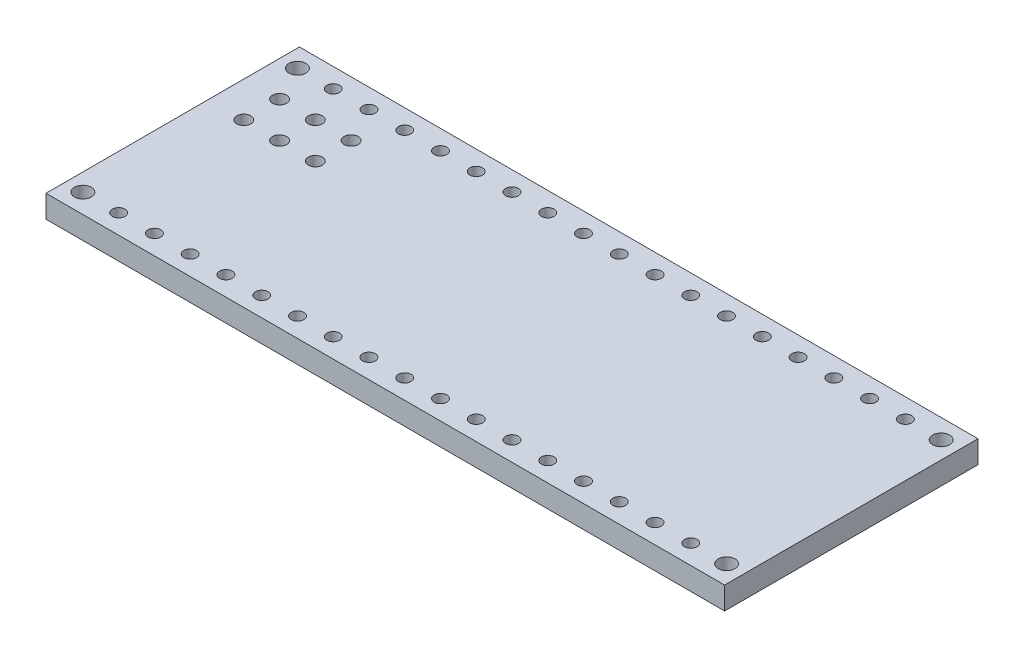
SolidWorks part; units mm, degrees
material "E-Glass Fiber"
ref_plane "Front Plane" through (0, 0, 0) normal (0, 0, 1) x (1, 0, 0)
ref_plane "Top Plane" through (0, 0, 0) normal (0, 1, 0) x (1, 0, 0)
ref_plane "Right Plane" through (0, 0, 0) normal (1, 0, 0) x (0, 0, -1)
sketch "Sketch1" plane through (0, 0, 0) normal (0, 1, 0) x (1, 0, 0)
  line L0 (0, 7.62) -> (-3.78, 7.62) construction
  line L1 (-3.78, 16.62) -> (44.42, 16.62)
  line L2 (-3.78, 16.62) -> (-3.78, -1.38)
  line L3 (-3.78, -1.38) -> (44.42, -1.38)
  line L4 (44.42, 16.62) -> (44.42, -1.38)
  line L5 (0, 0) -> (40.64, 0) construction
  line L6 (0, 0) -> (0, 15.24) construction
  line L7 (0, 15.24) -> (40.64, 15.24) construction
  line L8 (40.64, 0) -> (40.64, 15.24) construction
  line L10 (40.64, 7.62) -> (44.42, 7.62) construction
  circle A0 centre (-2.54, 0) radius 0.6
  circle A1 centre (-2.54, 15.24) radius 0.6
  circle A2 centre (43.18, 15.24) radius 0.6
  circle A3 centre (43.18, 0) radius 0.6
  dimension "D5" = 1.2
  dimension "D1" = 48.2
  dimension "D2" = 18
  dimension "D3" = 15.24
  dimension "D4" = 40.64
  dimension "D6" = 2.54
  dimension "D7" = 2.54
  dimension "D8" = 3.78
  dimension "D9" = 3.78
extrude "Boss-Extrude2" add sketch "Sketch1" along normal blind 1.6
sketch "Sketch2" plane through (0, 0, 0) normal (0, 1, 0) x (1, 0, 0)
  line L0 (0, -0.88) -> (0, 0.88) construction
  line L2 (-0.88, 0) -> (0.88, 0) construction
  circle A0 centre (0, 0) radius 0.45
  circle A1 centre (0, 15.24) radius 0.45
  dimension "D1" = 0.9
  dimension "D2" = 15.24
extrude "Cut-Extrude2" cut sketch "Sketch2" along normal blind 1.6
pattern_linear "LPattern1" count 17 spacing 2.54 along (1, 0, 0) of "Cut-Extrude2"
sketch "Sketch3" plane through (0, 0, 0) normal (0, 1, 0) x (1, 0, 0)
  line L1 (-0.88, 0) -> (0.88, 0) construction
  circle A0 centre (1.27, 12.7) radius 0.5
  circle A1 centre (-1.27, 12.7) radius 0.5
  circle A2 centre (-1.27, 10.16) radius 0.5
  circle A3 centre (3.81, 12.7) radius 0.5
  circle A4 centre (3.81, 10.16) radius 0.5
  circle A5 centre (1.27, 10.16) radius 0.5
  circle A6 centre (0, 15.24) radius 0.45 construction
  dimension "D1" = 1
  dimension "D5" = 10.16
  dimension "D7" = 2.54
  dimension "D2" = 2.54
  dimension "D3" = 2.54
  dimension "D4" = 1.27
  dimension "D6" = 2.54
extrude "Cut-Extrude4" cut sketch "Sketch3" along normal blind 1.6
ref_plane "Plane3" through (0, 0, -10.16) normal (0, 0, 1) x (1, 0, 0)
sketch "Sketch9" plane through (0, 0, 0) normal (0, 1, 0) x (1, 0, 0)
  line L0 (-2.53, 0) -> (2.53, 0) construction
  line L1 (44.42, -1.38) -> (44.42, 16.62) construction
  circle A0 centre (40.37, 5.42) radius 0.4
  circle A1 centre (40.37, 9.82) radius 0.4
  dimension "D1" = 0.8
  dimension "D2" = 4.4
  dimension "D3" = 5.42
  dimension "D4" = 4.05
extrude "Cut-Extrude6" [suppressed] cut sketch "Sketch9" along normal blind 10
